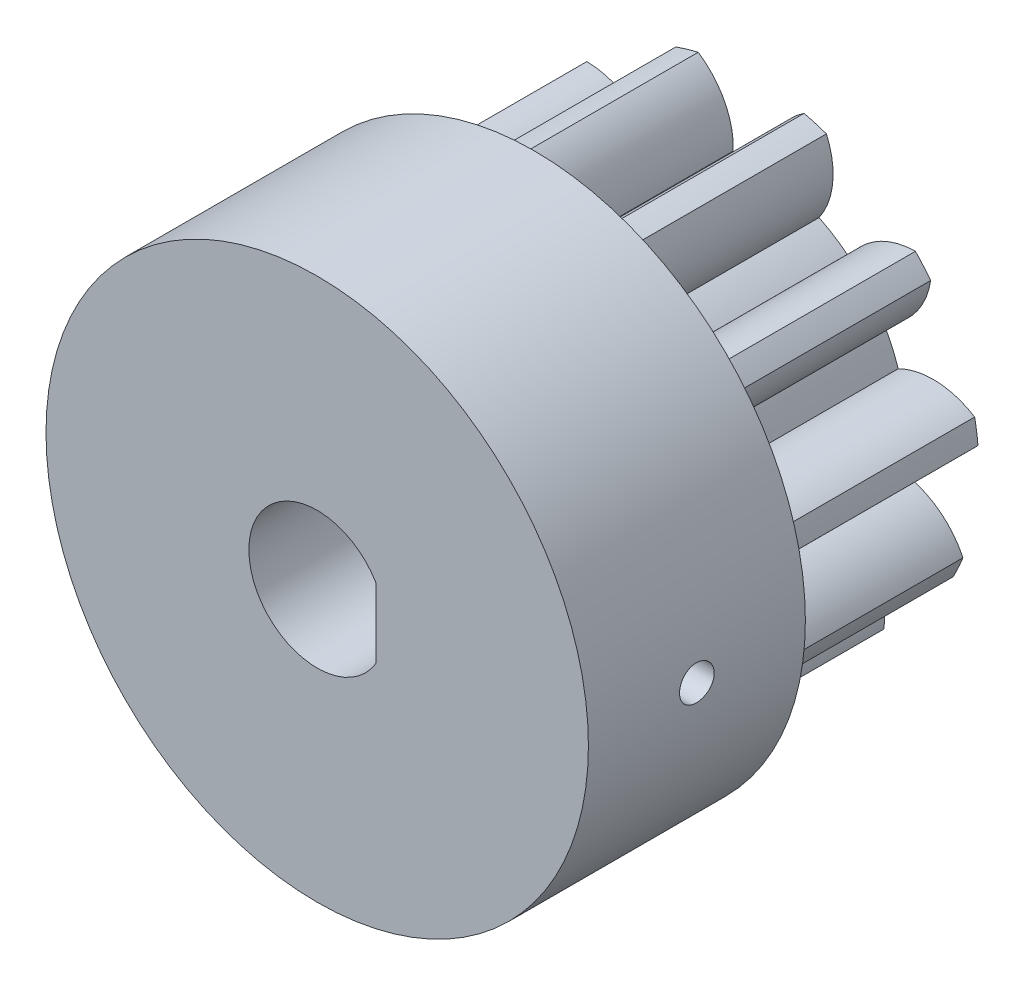
SolidWorks part; units mm, degrees
material "PMMA"
ref_plane "Front Plane" through (0, 0, 0) normal (0, 0, 1) x (1, 0, 0)
ref_plane "Top Plane" through (0, 0, 0) normal (0, 1, 0) x (1, 0, 0)
ref_plane "Right Plane" through (0, 0, 0) normal (1, 0, 0) x (0, 0, -1)
sketch "Sketch1" plane through (0, 0, 0) normal (1, 0, 0) x (0, 0, -1)
  line L1 (0, 0) -> (10, 0)
  line L2 (0, 0) -> (0, 10.5)
  line L3 (0, 10.5) -> (10, 10.5)
  line L4 (10, 0) -> (10, 10.5)
  dimension "D1" = 10.5
  dimension "D2" = 10
revolve "Revolve1" add sketch "Sketch1" angle 360 about L1
sketch "Sketch2" plane through (0, 0, 0) normal (0, 0, 1) x (1, 0, 0)
  line L0 (0, 0) -> (5.1764, 19.3185) construction
  line L1 (0, 0) -> (0, 20) construction
  line L2 (2.3294, 8.6933) -> (1.2842, 8.9734) construction
  circle A0 centre (0, 0) radius 10.5255 construction
  circle A1 centre (0, 0) radius 8.457 construction
  circle A2 centre (0, 0) radius 9 construction
  circle A3 centre (0, 0) radius 7.124 construction
  arc A4 (-0.8245, 7.0761) -> (0.8245, 7.0761) centre (0, 0) cw
  arc A5 (-2.4678, 10.2321) -> (2.4678, 10.2321) centre (0, 0) cw
  arc A6 (-2.4678, 10.2321) -> (-0.8245, 7.0761) centre (-4.4221, 7.2087) cw
  arc A7 (2.4678, 10.2321) -> (0.8245, 7.0761) centre (4.4221, 7.2087) ccw
  point P10 (0, 7.124)
  point P13 (0, 10.5255)
  dimension "D1" = 21.051
  dimension "D2" = 16.914
  dimension "D3" = 18
  dimension "D4" = 14.248
  dimension "D7" = 3.6
  dimension "D5" = 15
  dimension "D6" = 20
  dimension "D8" = 1.082
extrude "Cut-Extrude1" cut sketch "Sketch2" against normal through all
pattern_circular "CirPattern1" count 11 over 360 about axis through (0, 0, 0) along (0, 0, 1) of "Cut-Extrude1"
sketch "Sketch3" plane through (0, 0, 0) normal (0, 0, 1) x (1, 0, 0)
  circle A0 centre (0, 0) radius 12.5
  dimension "D1" = 25
extrude "Boss-Extrude1" add sketch "Sketch3" along normal blind 10
sketch "Sketch4" plane through (0, 0, 10) normal (0, 0, 1) x (1, 0, 0)
  line L0 (2.7, 1.6225) -> (2.7, -1.6225)
  line L1 (-3.15, 0) -> (2.7, 0) construction
  arc A0 (2.7, 1.6225) -> (2.7, -1.6225) centre (0, 0) ccw
  dimension "D1" = 6.3
  dimension "D2" = 5.85
extrude "Cut-Extrude2" cut sketch "Sketch4" against normal through all
ref_plane "Plane1" through (12.5, 0, 0) normal (1, 0, 0) x (0, 0, -1)
hole_wizard "M2 Tapped Hole1" positions "Sketch5" profile "Sketch6" tap size "M2" standard "ISO" end condition up to next
sketch "Sketch5" plane through (12.5, 0, 0) normal (1, 0, 0) x (0, 0, -1)
  point P0 (-5, 0)
  dimension "D1" = 5
sketch "Sketch6" plane through (12.5, 0, 5) normal (0, 1, 0) x (0, 0, -1)
  line L0 (0, 0) -> (0, 9.8)
  line L1 (0, 9.8) -> (0.8, 9.8)
  line L2 (0.8, 9.8) -> (0.8, 0)
  line L5 (0.8, 0) -> (0, 0)
  line L11 (0, -6.35) -> (0, 107.95) construction
  dimension "Thru Tap Drill Dia." = 1.6
  dimension "Thru Tap Drill Depth" = 9.8
cosmetic thread "Hole Thread2" parameters "D2"=2
